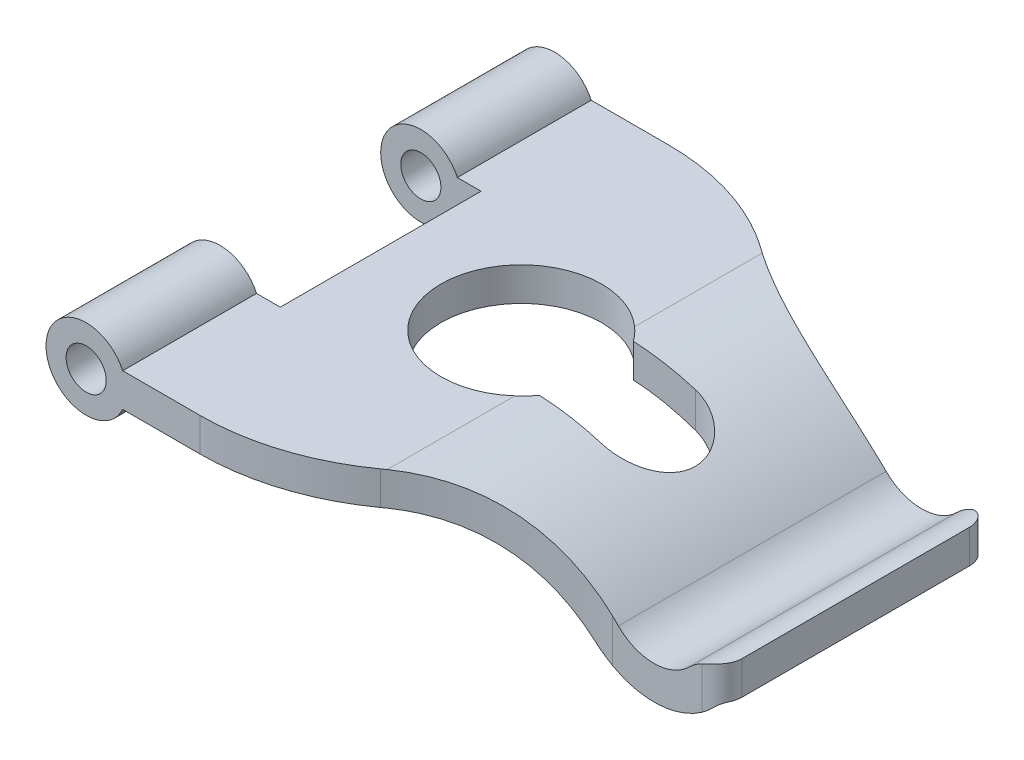
SolidWorks part; units mm, degrees
ref_plane "Front Plane" through (0, 0, 0) normal (0, 0, 1) x (1, 0, 0)
ref_plane "Top Plane" through (0, 0, 0) normal (0, 1, 0) x (1, 0, 0)
ref_plane "Right Plane" through (0, 0, 0) normal (1, 0, 0) x (0, 0, -1)
sketch "Sketch1" plane through (0, 0, 0) normal (0, 0, 1) x (1, 0, 0)
  line L0 (80, -13.3647) -> (60.4139, 6.2214) construction
  line L1 (6, 0) -> (38, 0) construction
  line L2 (80, -8.9647) -> (80, 29.7243) construction
  line L3 (38, 0) -> (38, -49.8744) construction
  line L4 (38, -35) -> (88.0366, 15.0366) construction
  line L5 (6, -2.5) -> (38, -2.5)
  line L6 (6, 2.5) -> (38, 2.5)
  line L7 (6, 2.5) -> (5.4544, 2.5)
  line L8 (6, -2.5) -> (5.4544, -2.5)
  line L9 (80, -6.4647) -> (80, -11.4647)
  arc A0 (5.4544, 2.5) -> (5.4544, -2.5) centre (0, 0) ccw
  circle A1 centre (0, 0) radius 3
  arc A2 (38, 0) -> (62.7487, -10.2513) centre (38, -35) cw construction
  arc A3 (62.7487, -10.2513) -> (76.8894, -10.2528) centre (69.8198, -3.1802) ccw construction
  arc A4 (76.8894, -10.2528) -> (80, -8.9647) centre (80, -13.3647) cw construction
  arc A5 (38, -2.5) -> (60.981, -12.019) centre (38, -35) cw
  arc A6 (60.981, -12.019) -> (78.6568, -12.0209) centre (69.8198, -3.1802) ccw
  arc A7 (78.6568, -12.0209) -> (80, -11.4647) centre (80, -13.3647) cw
  arc A8 (38, 2.5) -> (64.5165, -8.4835) centre (38, -35) cw
  arc A9 (64.5165, -8.4835) -> (75.122, -8.4846) centre (69.8198, -3.1802) ccw
  arc A10 (75.122, -8.4846) -> (80, -6.4647) centre (80, -13.3647) cw
  point P7 (0, 0)
  dimension "D1" = 12
  dimension "D2" = 6
  dimension "D6" = 35
  dimension "D7" = 45
  dimension "D8" = 4.4
  dimension "D3" = 10
  dimension "D4" = 38
  dimension "D5" = 80
  dimension "D9" = 90
  dimension "D10" = 45
  dimension "D11" = 2.5
  dimension "D12" = 2.5
extrude "Boss-Extrude1" add sketch "Sketch1" along normal mid plane 70
sketch "Sketch2" plane through (0, 2.5, 0) normal (0, 1, 0) x (1, 0, 0)
  line L0 (-6, 35) -> (-6, -35) construction
  line L1 (-6, 15) -> (9, 15)
  line L2 (-6, 15) -> (-6, -15)
  line L3 (-6, -15) -> (9, -15)
  line L4 (9, 15) -> (9, -15)
  line L5 (-6, -35) -> (5.4544, -35) construction
  dimension "D1" = 30
  dimension "D2" = 20
  dimension "D3" = 15
extrude "Cut-Extrude2" cut sketch "Sketch2" against normal through all both and the other way through all
sketch "Sketch3" plane through (0, 2.5, 0) normal (0, 1, 0) x (1, 0, 0)
  line L0 (0, 35) -> (30, 35) construction
  line L1 (3, 35) -> (-3, 35) construction
  line L2 (38, 35) -> (5.4544, 35) construction
  line L3 (42, 0) -> (49, 0) construction
  line L4 (39.7468, 7) -> (49, 7)
  line L5 (39.7468, -7) -> (49, -7)
  arc A0 (39.7468, 7) -> (39.7468, -7) centre (30, 0) ccw
  arc A2 (49, -7) -> (49, 7) centre (49, 0) ccw
  point P10 (39.5, 0)
  dimension "D2" = 24
  dimension "D4" = 7
  dimension "D1" = 30
  dimension "D3" = 19
extrude "Cut-Extrude3" cut sketch "Sketch3" against normal through all both and the other way through all
sketch "Sketch4" plane through (0, 2.5, 0) normal (0, 1, 0) x (1, 0, 0)
  line L0 (38, -35) -> (5.4544, -35) construction
  line L2 (80, -35) -> (80, 35) construction
  line L3 (3, 35) -> (-3, 35) construction
  line L4 (80, -20) -> (63.6369, -20)
  line L5 (80, -20) -> (80, -35)
  line L6 (80, -35) -> (17, -35)
  line L7 (0, 0) -> (123.6264, 0) construction
  line L8 (80, 20) -> (63.6369, 20)
  line L9 (80, 20) -> (80, 35)
  line L10 (80, 35) -> (17, 35)
  arc A0 (17, -35) -> (37.4036, -28.4375) centre (17, 0) ccw
  arc A1 (63.6369, -20) -> (37.4036, -28.4375) centre (63.6369, -65) ccw
  arc A2 (63.6369, 20) -> (37.4036, 28.4375) centre (63.6369, 65) cw
  arc A3 (37.4036, 28.4375) -> (17, 35) centre (17, 0) ccw
  point P11 (80, 0)
  point P12 (0, 35)
  dimension "D2" = 90
  dimension "D3" = 70
  dimension "D1" = 40
  dimension "D4" = 17
  dimension "D5" = 65
extrude "Cut-Extrude5" cut sketch "Sketch4" against normal through all both
fillet "Fillet2" radius 3 2 edges at (80, -8.9647, -20) (80, -8.9647, 20)
